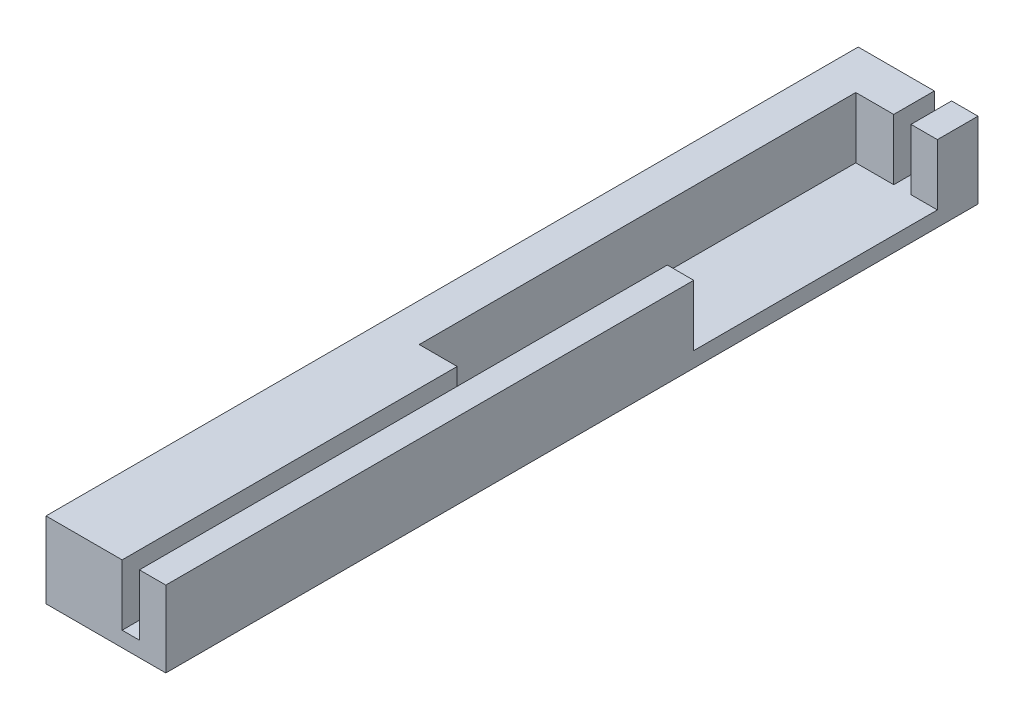
SolidWorks part; units mm, degrees
ref_plane "Front Plane" through (0, 0, 0) normal (0, 0, 1) x (1, 0, 0)
ref_plane "Top Plane" through (0, 0, 0) normal (0, 1, 0) x (1, 0, 0)
ref_plane "Right Plane" through (0, 0, 0) normal (1, 0, 0) x (0, 0, -1)
sketch "Sketch1" plane through (0, 0, 0) normal (0, 1, 0) x (1, 0, 0)
  line L1 (-3.762, 1.9862) -> (8.038, 1.9862)
  line L2 (-3.762, 1.9862) -> (-3.762, -78.0138)
  line L3 (-3.762, -78.0138) -> (8.038, -78.0138)
  line L4 (8.038, 1.9862) -> (8.038, -78.0138)
  dimension "D1" = 11.8
  dimension "D2" = 80
extrude "Boss-Extrude1" add sketch "Sketch1" along normal blind 1.5
sketch "Sketch2" plane through (0, 1.5, 0) normal (0, 1, 0) x (1, 0, 0)
  line L0 (8.038, 1.9862) -> (-3.762, 1.9862) construction
  line L1 (-3.762, 1.9862) -> (3.738, 1.9862)
  line L2 (-3.762, 1.9862) -> (-3.762, -78.0138)
  line L3 (-3.762, -78.0138) -> (3.738, -78.0138)
  line L4 (3.738, 1.9862) -> (3.738, -78.0138)
  line L5 (-3.762, -78.0138) -> (8.038, -78.0138) construction
  line L6 (-3.762, 1.9862) -> (-3.762, -78.0138) construction
  line L8 (5.438, 1.9862) -> (8.038, 1.9862)
  line L9 (5.438, 1.9862) -> (5.438, -78.0138)
  line L10 (5.438, -78.0138) -> (8.038, -78.0138)
  line L11 (8.038, 1.9862) -> (8.038, -78.0138)
  dimension "D1" = 0
  dimension "D2" = 7.5
  dimension "D3" = 1.7
extrude "Boss-Extrude2" add sketch "Sketch2" along normal blind 6
sketch "Sketch3" plane through (0, 7.5, 0) normal (0, 1, 0) x (1, 0, 0)
  line L0 (3.738, -78.0138) -> (3.738, 1.9862) construction
  line L1 (3.738, -2.0138) -> (0, -2.0138)
  line L2 (3.738, -2.0138) -> (3.738, -45.0138)
  line L3 (3.738, -45.0138) -> (0, -45.0138)
  line L4 (0, -2.0138) -> (0, -45.0138)
  line L5 (5.438, 1.9862) -> (5.438, -78.0138) construction
  line L6 (5.438, -2.0138) -> (8.038, -2.0138)
  line L7 (5.438, -2.0138) -> (5.438, -26.0138)
  line L8 (5.438, -26.0138) -> (8.038, -26.0138)
  line L9 (8.038, -2.0138) -> (8.038, -26.0138)
  line L10 (8.038, -78.0138) -> (8.038, 1.9862) construction
  line L11 (8.038, 1.9862) -> (5.438, 1.9862) construction
  line L12 (3.738, 1.9862) -> (-3.762, 1.9862) construction
  line L13 (5.438, -78.0138) -> (8.038, -78.0138) construction
  line L14 (-3.762, -78.0138) -> (3.738, -78.0138) construction
  point P20 (1.869, -45.0138)
  dimension "D1" = 4
  dimension "D2" = 4
  dimension "D3" = 52
  dimension "D4" = 33
extrude "Cut-Extrude1" cut sketch "Sketch3" against normal up to surface (6 mm away) up to face at (4.588, 1.5, 38.0138)
